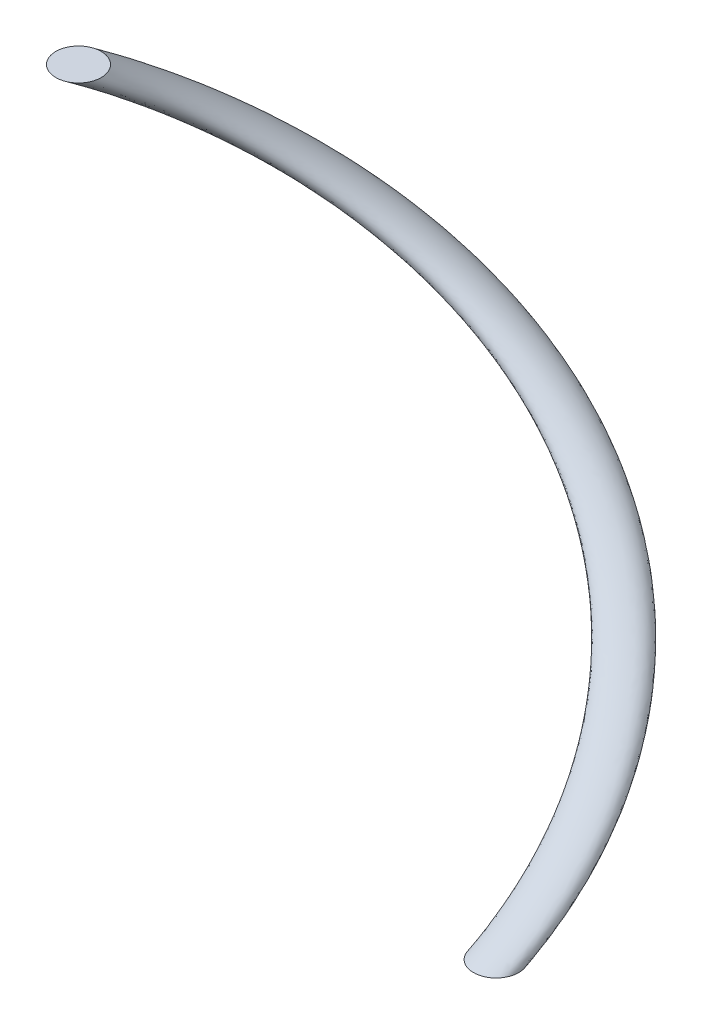
SolidWorks part; units mm, degrees
ref_plane "Front Plane" through (0, 0, 0) normal (0, 0, 1) x (1, 0, 0)
ref_plane "Top Plane" through (0, 0, 0) normal (0, 1, 0) x (1, 0, 0)
ref_plane "Right Plane" through (0, 0, 0) normal (1, 0, 0) x (0, 0, -1)
sketch "Sketch1" plane through (0, 0, 0) normal (0, 1, 0) x (1, 0, 0)
  line L1 (20, -4) -> (24, -4) construction
  line L2 (20, -4) -> (20, 0) construction
  line L3 (20, 0) -> (24, 0) construction
  line L4 (24, -4) -> (24, 0) construction
  line L5 (22, 0) -> (22, -4) construction
  line L6 (20, -2) -> (24, -2) construction
  circle A0 centre (0, 0) radius 20 construction
  circle A1 centre (22, -2) radius 2
  point P360 (22, -2)
  dimension "D1" = 4
  dimension "D2" = 4
  dimension "D3" = 20
sketch "Sketch2" plane through (0, 0, 0) normal (0, 1, 0) x (1, 0, 0)
  circle A0 centre (0, 0) radius 15
  dimension "D1" = 30
curve "Helix/Spiral1" pitch 90 height 43.2 turns 0.48
sweep "Sweep1" add profiles "Sketch1" path "Helix/Spiral1"
